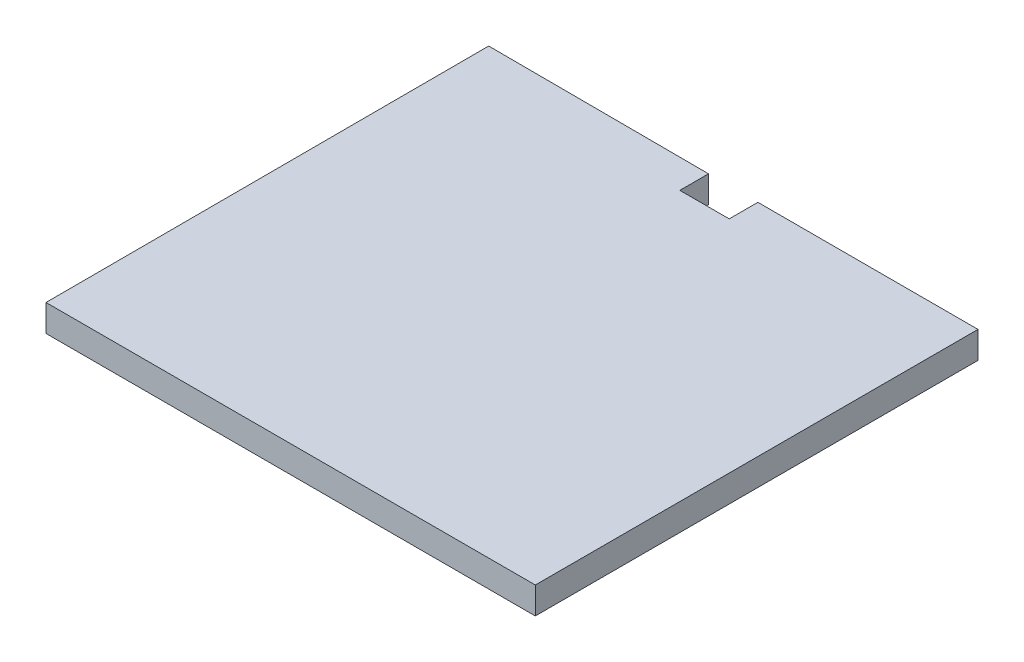
SolidWorks part; units mm, degrees
ref_plane "Front Plane" through (0, 0, 0) normal (0, 0, 1) x (1, 0, 0)
ref_plane "Top Plane" through (0, 0, 0) normal (0, 1, 0) x (1, 0, 0)
ref_plane "Right Plane" through (0, 0, 0) normal (1, 0, 0) x (0, 0, -1)
sketch "Sketch2" plane through (0, 92.0764, 0) normal (0, 1, 0) x (1, 0, 0)
  line L0 (-11.2134, -6.8261) -> (-11.2134, 5.7868)
  line L1 (-11.2134, 5.7868) -> (-108.2045, 6.1202)
  line L2 (-108.2045, 6.1202) -> (-107.8711, -188.8798)
  line L3 (-107.8711, -188.8798) -> (107.2955, -188.8798)
  line L4 (107.2955, -188.8798) -> (107.2955, 5.7868)
  line L5 (107.2955, -188.8798) -> (107.2955, 5.7868) construction
  line L6 (107.2955, 5.7868) -> (10.5048, 5.7868)
  line L7 (107.2955, 5.7868) -> (10.5048, 5.7868) construction
  line L8 (10.5048, 5.7868) -> (10.5048, -6.8261) construction
  line L9 (10.5048, 5.7868) -> (10.5048, -6.8261)
  line L10 (10.5048, -6.8261) -> (-11.2134, -6.8261)
extrude "Boss-Extrude1" add sketch "Sketch2" along normal blind 11.811
